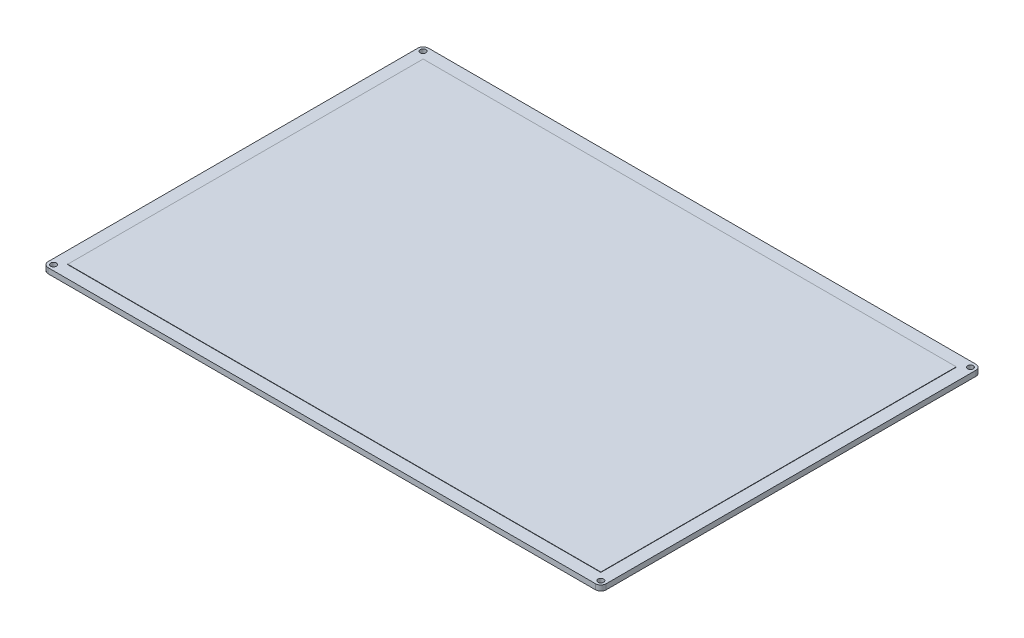
SolidWorks part; units mm, degrees
ref_plane "Front Plane" through (0, 0, 0) normal (0, 0, 1) x (1, 0, 0)
ref_plane "Top Plane" through (0, 0, 0) normal (0, 1, 0) x (1, 0, 0)
ref_plane "Right Plane" through (0, 0, 0) normal (1, 0, 0) x (0, 0, -1)
ref_plane "Plane1" through (0, 3, 0) normal (0, 1, 0) x (1, 0, 0)
sketch "Sketch1" plane through (0, 3, 0) normal (0, 1, 0) x (1, 0, 0)
  line L0 (157, 107) -> (-157, 107)
  line L1 (-157, 107) -> (-157, -107)
  line L2 (-157, -107) -> (157, -107)
  line L3 (157, -107) -> (157, 107)
extrude "Boss-Extrude1" add sketch "Sketch1" against normal blind 3
sketch "Sketch2" plane through (0, 3, 0) normal (0, 1, 0) x (-1, 0, 0)
  line L0 (150, -100) -> (-150, -100)
  line L1 (-150, -100) -> (-150, 100)
  line L2 (-150, 100) -> (150, 100)
  line L3 (150, 100) -> (150, -100)
extrude "Boss-Extrude2" add sketch "Sketch2" along normal blind 0.2
hole_wizard "Ø3.2 (3.2) Diameter Hole1" positions "Sketch4" profile "Sketch3" hole size "Ø3.2" standard "ANSI Metric"
sketch "Sketch4" plane through (0, 3, 0) normal (0, 1, 0) x (1, 0, 0)
  point P0 (154, -104)
  point P1 (-154, -104)
  point P2 (154, 104)
  point P3 (-154, 104)
sketch "Sketch3" plane through (154, 3, 104) normal (1, 0, 0) x (0, 0, 1)
  line L0 (0, 0) -> (0, 3)
  line L1 (0, 3) -> (1.6, 3)
  line L2 (1.6, 3) -> (1.6, 0)
  line L5 (1.6, 0) -> (0, 0)
  line L11 (0, -6.35) -> (0, 107.95) construction
  dimension "Thru Hole Dia." = 3.2
  dimension "Thru Hole Depth" = 3
fillet "Fillet1" radius 3 4 edges at (-157, 1.5, 107) (157, 1.5, 107) (-157, 1.5, -107) (157, 1.5, -107)
